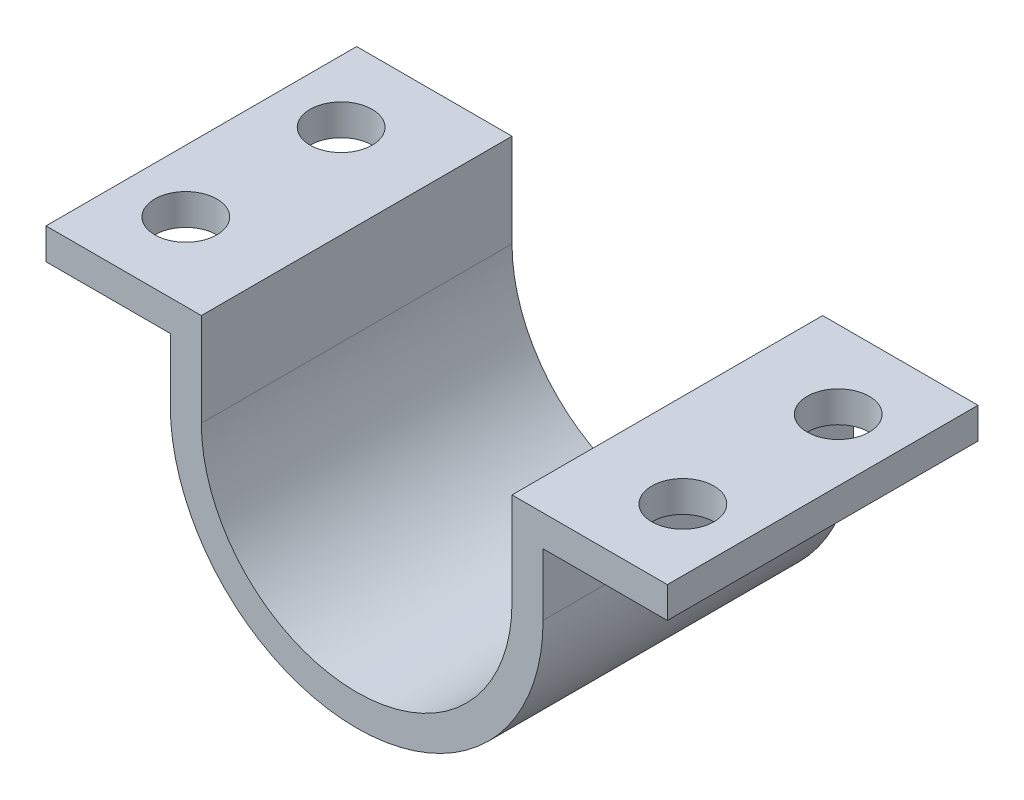
SolidWorks part; units mm, degrees
ref_plane "Front Plane" through (0, 0, 0) normal (0, 0, 1) x (1, 0, 0)
ref_plane "Top Plane" through (0, 0, 0) normal (0, 1, 0) x (1, 0, 0)
ref_plane "Right Plane" through (0, 0, 0) normal (1, 0, 0) x (0, 0, -1)
sketch "Sketch1" plane through (0, 0, 0) normal (0, 0, 1) x (1, 0, 0)
  line L0 (-50, 15) -> (-25, 15)
  line L1 (-25, 15) -> (-25, 0)
  line L2 (25, 0) -> (25, 15)
  line L3 (25, 15) -> (50, 15)
  line L4 (-50, 10) -> (-30, 10)
  line L5 (-30, 10) -> (-30, 0)
  line L6 (30, 0) -> (30, 10)
  line L7 (30, 10) -> (50, 10)
  line L8 (-50, 15) -> (-50, 10)
  line L9 (50, 15) -> (50, 10)
  arc A0 (-25, 0) -> (25, 0) centre (0, 0) ccw
  arc A1 (-30, 0) -> (30, 0) centre (0, 0) ccw
  point P14 (0, 0)
  point P15 (47.9049, 19.1807)
  point P17 (-48.092, 21.052)
  point P18 (-25, 20.8648)
  point P19 (-55.0158, 16.3737)
  point P20 (-58.0098, 15.8124)
  point P21 (-50, 18.245)
  dimension "D1" = 5
  dimension "D2" = 50
  dimension "D3" = 25
  dimension "D4" = 10
extrude "Boss-Extrude1" add sketch "Sketch1" along normal blind 50
sketch "Sketch2" plane through (0, 10, 0) normal (0, -1, 0) x (1, 0, 0)
  line L0 (0, 0) -> (0, 55.8355) construction
  line L1 (40, 25) -> (40, 37.5) construction
  line L2 (-50, 25) -> (50, 25) construction
  line L3 (-50, 50) -> (-50, 0) construction
  line L4 (50, 50) -> (50, 0) construction
  line L5 (40, 37.5) -> (40, 50) construction
  line L7 (30, 50) -> (50, 50) construction
  circle A0 centre (40, 37.5) radius 5
  circle A1 centre (40, 12.5) radius 5
  circle A2 centre (-40, 12.5) radius 5
  circle A3 centre (-40, 37.5) radius 5
  point P18 (40, 50)
  dimension "D1" = 10
extrude "Cut-Extrude1" cut sketch "Sketch2" against normal through all
